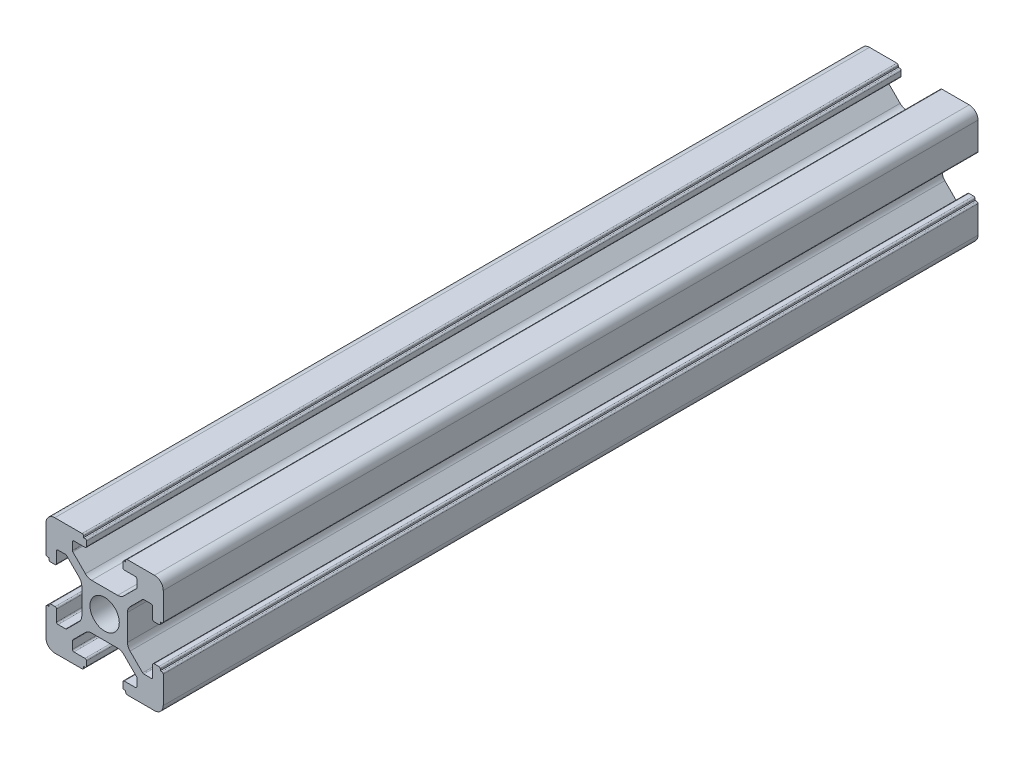
SolidWorks part; units mm, degrees
ref_plane "前视基准面" through (0, 0, 0) normal (0, 0, 1) x (1, 0, 0)
ref_plane "上视基准面" through (0, 0, 0) normal (0, 1, 0) x (1, 0, 0)
ref_plane "右视基准面" through (0, 0, 0) normal (1, 0, 0) x (0, 0, -1)
sketch "草图1" plane through (0, 0, 0) normal (0, 0, 1) x (1, 0, 0)
  line L0 (0, 0) -> (0, 5.5) construction
  line L1 (-8.5023, -10.0023) -> (-3.85, -10.0023)
  line L2 (-10.0023, -8.5023) -> (-10.0023, -3.85)
  line L3 (-8.5023, 10.0023) -> (-3.85, 10.0023)
  line L4 (10.0023, -8.5023) -> (10.0023, -3.85)
  line L5 (-10.0023, -10.0023) -> (10.0023, 10.0023) construction
  line L6 (-10.0023, 10.0023) -> (10.0023, -10.0023) construction
  line L7 (-2.218, -3.9) -> (2.218, -3.9)
  line L8 (-3.9, -2.218) -> (-3.9, 2.218)
  line L9 (-2.218, 3.9) -> (2.218, 3.9)
  line L10 (3.9, -2.218) -> (3.9, 2.218)
  line L11 (-3.9, -3.9) -> (3.9, 3.9) construction
  line L12 (-3.9, 3.9) -> (3.9, -3.9) construction
  line L13 (-5.25, -8.2) -> (-3.35, -8.2)
  line L14 (-8.2, -5.25) -> (-8.2, -3.35)
  line L15 (-5.25, 8.2) -> (-3.35, 8.2)
  line L16 (8.2, -5.25) -> (8.2, -3.35)
  line L17 (-8.2, -8.2) -> (8.2, 8.2) construction
  line L18 (-8.2, 8.2) -> (8.2, -8.2) construction
  line L19 (-7.95, 5.5) -> (-6.6642, 5.5)
  line L20 (0, 0) -> (5.5, 0) construction
  line L23 (-5.5, 7.95) -> (-5.5, 6.6642)
  line L26 (0, 0) -> (-0.5303, 0.5303)
  line L27 (3.2787, 4.3393) -> (5.4268, 6.4874)
  line L28 (0, 0) -> (0.5303, -0.5303)
  line L29 (5.5, 6.6642) -> (5.5, 7.95)
  line L30 (4.3393, 3.2787) -> (6.4874, 5.4268)
  line L31 (6.6642, 5.5) -> (7.95, 5.5)
  line L32 (4.3393, -3.2787) -> (6.4874, -5.4268)
  line L33 (3.2787, -4.3393) -> (5.4268, -6.4874)
  line L34 (-3.2787, -4.3393) -> (-5.4268, -6.4874)
  line L35 (-4.3393, -3.2787) -> (-6.4874, -5.4268)
  line L36 (-4.3393, 3.2787) -> (-6.4874, 5.4268)
  line L37 (-3.2787, 4.3393) -> (-5.4268, 6.4874)
  line L38 (3.1, -8.45) -> (3.1, -9.2523)
  line L39 (8.45, 3.1) -> (9.2523, 3.1)
  line L40 (-5.5, -6.6642) -> (-5.5, -7.95)
  line L41 (-6.6642, -5.5) -> (-7.95, -5.5)
  line L42 (5.5, -6.6642) -> (5.5, -7.95)
  line L43 (6.6642, -5.5) -> (7.95, -5.5)
  line L44 (9.2523, -3.1) -> (8.45, -3.1)
  line L46 (10.0023, 3.85) -> (10.0023, 8.5023)
  line L47 (8.2, 3.35) -> (8.2, 5.25)
  line L48 (-3.1, -9.2523) -> (-3.1, -8.45)
  line L49 (-8.45, -3.1) -> (-9.2523, -3.1)
  line L50 (-9.2523, 3.1) -> (-8.45, 3.1)
  line L51 (-3.1, 8.45) -> (-3.1, 9.2523)
  line L52 (3.1, 9.2523) -> (3.1, 8.45)
  line L53 (3.85, 10.0023) -> (8.5023, 10.0023)
  line L54 (3.35, 8.2) -> (5.25, 8.2)
  line L55 (-10.0023, 3.85) -> (-10.0023, 8.5023)
  line L56 (-8.2, 3.35) -> (-8.2, 5.25)
  line L57 (3.35, -8.2) -> (5.25, -8.2)
  line L58 (3.85, -10.0023) -> (8.5023, -10.0023)
  line L59 (9.7523, -3.6) -> (9.5023, -3.6)
  line L61 (9.7523, 3.6) -> (9.5023, 3.6)
  line L62 (9.5023, -3.6) -> (9.5023, -3.35)
  line L63 (3.6, -9.7523) -> (3.6, -9.5023)
  line L64 (3.35, -9.5023) -> (3.6, -9.5023)
  line L65 (9.5023, 3.35) -> (9.5023, 3.6)
  line L66 (-3.6, -9.5023) -> (-3.35, -9.5023)
  line L67 (-3.6, -9.7523) -> (-3.6, -9.5023)
  line L68 (-9.7523, -3.6) -> (-9.5023, -3.6)
  line L69 (-9.5023, -3.35) -> (-9.5023, -3.6)
  line L70 (-9.5023, 3.6) -> (-9.5023, 3.35)
  line L71 (-9.7523, 3.6) -> (-9.5023, 3.6)
  line L72 (-3.6, 9.7523) -> (-3.6, 9.5023)
  line L73 (-3.35, 9.5023) -> (-3.6, 9.5023)
  line L74 (3.6, 9.5023) -> (3.35, 9.5023)
  line L75 (3.6, 9.7523) -> (3.6, 9.5023)
  circle A0 centre (0, 0) radius 2.5
  arc A1 (10.0023, 8.5023) -> (8.5023, 10.0023) centre (8.5023, 8.5023) ccw
  arc A2 (8.5023, -10.0023) -> (10.0023, -8.5023) centre (8.5023, -8.5023) ccw
  arc A3 (-10.0023, -8.5023) -> (-8.5023, -10.0023) centre (-8.5023, -8.5023) ccw
  arc A4 (-10.0023, 8.5023) -> (-8.5023, 10.0023) centre (-8.5023, 8.5023) cw
  arc A5 (-9.5023, -3.35) -> (-9.2523, -3.1) centre (-9.2523, -3.35) cw
  arc A6 (-9.7523, -3.6) -> (-10.0023, -3.85) centre (-9.7523, -3.85) ccw
  arc A7 (-8.45, -3.1) -> (-8.2, -3.35) centre (-8.45, -3.35) cw
  arc A8 (-7.95, -5.5) -> (-8.2, -5.25) centre (-7.95, -5.25) cw
  arc A9 (-6.4874, -5.4268) -> (-6.6642, -5.5) centre (-6.6642, -5.25) cw
  arc A10 (-5.4268, -6.4874) -> (-5.5, -6.6642) centre (-5.25, -6.6642) ccw
  arc A11 (-5.5, -7.95) -> (-5.25, -8.2) centre (-5.25, -7.95) ccw
  arc A12 (-3.6, -9.7523) -> (-3.85, -10.0023) centre (-3.85, -9.7523) cw
  arc A13 (-3.35, -9.5023) -> (-3.1, -9.2523) centre (-3.35, -9.2523) ccw
  arc A14 (-3.1, -8.45) -> (-3.35, -8.2) centre (-3.35, -8.45) ccw
  arc A15 (3.1, -8.45) -> (3.35, -8.2) centre (3.35, -8.45) cw
  arc A16 (5.5, -7.95) -> (5.25, -8.2) centre (5.25, -7.95) cw
  arc A17 (5.4268, -6.4874) -> (5.5, -6.6642) centre (5.25, -6.6642) cw
  arc A18 (6.4874, -5.4268) -> (6.6642, -5.5) centre (6.6642, -5.25) ccw
  arc A19 (7.95, -5.5) -> (8.2, -5.25) centre (7.95, -5.25) ccw
  arc A20 (8.45, -3.1) -> (8.2, -3.35) centre (8.45, -3.35) ccw
  arc A21 (9.5023, -3.35) -> (9.2523, -3.1) centre (9.2523, -3.35) ccw
  arc A22 (9.7523, -3.6) -> (10.0023, -3.85) centre (9.7523, -3.85) cw
  arc A23 (3.35, -9.5023) -> (3.1, -9.2523) centre (3.35, -9.2523) cw
  arc A24 (3.6, -9.7523) -> (3.85, -10.0023) centre (3.85, -9.7523) ccw
  arc A25 (7.95, 5.5) -> (8.2, 5.25) centre (7.95, 5.25) cw
  arc A26 (8.2, 3.35) -> (8.45, 3.1) centre (8.45, 3.35) ccw
  arc A27 (9.5023, 3.35) -> (9.2523, 3.1) centre (9.2523, 3.35) cw
  arc A28 (9.7523, 3.6) -> (10.0023, 3.85) centre (9.7523, 3.85) ccw
  arc A29 (6.6642, 5.5) -> (6.4874, 5.4268) centre (6.6642, 5.25) ccw
  arc A30 (5.4268, 6.4874) -> (5.5, 6.6642) centre (5.25, 6.6642) ccw
  arc A31 (5.5, 7.95) -> (5.25, 8.2) centre (5.25, 7.95) ccw
  arc A32 (3.1, 8.45) -> (3.35, 8.2) centre (3.35, 8.45) ccw
  arc A33 (3.6, 9.7523) -> (3.85, 10.0023) centre (3.85, 9.7523) cw
  arc A34 (3.35, 9.5023) -> (3.1, 9.2523) centre (3.35, 9.2523) ccw
  arc A35 (-9.7523, 3.6) -> (-10.0023, 3.85) centre (-9.7523, 3.85) cw
  arc A36 (-9.5023, 3.35) -> (-9.2523, 3.1) centre (-9.2523, 3.35) ccw
  arc A37 (-8.45, 3.1) -> (-8.2, 3.35) centre (-8.45, 3.35) ccw
  arc A38 (-8.2, 5.25) -> (-7.95, 5.5) centre (-7.95, 5.25) cw
  arc A39 (-6.4874, 5.4268) -> (-6.6642, 5.5) centre (-6.6642, 5.25) ccw
  arc A40 (-5.4268, 6.4874) -> (-5.5, 6.6642) centre (-5.25, 6.6642) cw
  arc A41 (-5.5, 7.95) -> (-5.25, 8.2) centre (-5.25, 7.95) cw
  arc A42 (-3.1, 8.45) -> (-3.35, 8.2) centre (-3.35, 8.45) cw
  arc A43 (-3.1, 9.2523) -> (-3.35, 9.5023) centre (-3.35, 9.2523) ccw
  arc A44 (-3.6, 9.7523) -> (-3.85, 10.0023) centre (-3.85, 9.7523) ccw
  arc A45 (-4.3393, 3.2787) -> (-3.9, 2.218) centre (-5.4, 2.218) cw
  arc A46 (-3.2787, 4.3393) -> (-2.218, 3.9) centre (-2.218, 5.4) ccw
  arc A47 (3.2787, 4.3393) -> (2.218, 3.9) centre (2.218, 5.4) cw
  arc A48 (4.3393, 3.2787) -> (3.9, 2.218) centre (5.4, 2.218) ccw
  arc A49 (4.3393, -3.2787) -> (3.9, -2.218) centre (5.4, -2.218) cw
  arc A50 (3.2787, -4.3393) -> (2.218, -3.9) centre (2.218, -5.4) ccw
  arc A51 (-4.3393, -3.2787) -> (-3.9, -2.218) centre (-5.4, -2.218) ccw
  arc A52 (-2.218, -3.9) -> (-3.2787, -4.3393) centre (-2.218, -5.4) ccw
  point P0 (0, 0)
  point P7 (10.0023, 0)
  point P62 (0, 0)
  point P76 (0, 0)
  point P92 (-8.2, -5.5)
  point P99 (0, 0)
  point P106 (-5.5, -8.2)
  point P117 (5.5, -8.2)
  point P124 (8.2, -5.5)
  point P137 (8.2, 5.5)
  point P140 (8.2, 3.1)
  point P147 (6.5607, 5.5)
  point P152 (5.5, 8.2)
  point P167 (-8.2, 5.5)
  point P174 (-5.5, 8.2)
  dimension "D1" = 1.5
  dimension "D5" = 0.25
  dimension "D6" = 1.5
  dimension "D2" = 4
  dimension "D3" = 4
  dimension "D4" = 4
extrude "凸台-拉伸1" add sketch "草图1" along normal blind 139 contours A52 L7 A50 L33 A17 L42 A16 L57 A15 L38 A23 L64 L63 A24 L58 A2 L4 A22 L59 L62 A21 L44 A20 L16 A19 L43 A18 L32 A49 L10 A48 L30 A29 L31 A25 L47 A26 L39 A27 L65 L61 A28 L46 A1 L53 A33 L75 L74 A34 L52 A32
ref_plane "Plane1" through (0, 0, 69.5) normal (0, 0, 1) x (1, 0, 0)
